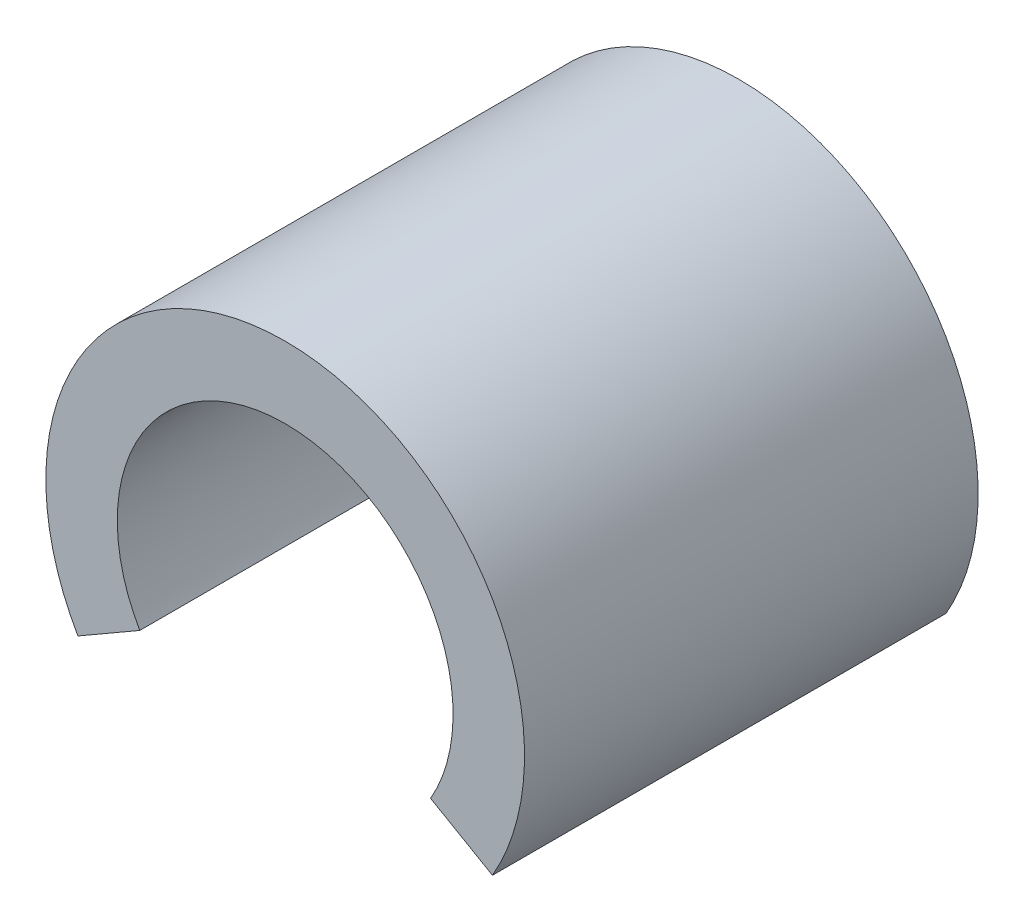
SolidWorks part; units mm, degrees
ref_plane "Front Plane" through (0, 0, 0) normal (0, 0, 1) x (1, 0, 0)
ref_plane "Top Plane" through (0, 0, 0) normal (0, 1, 0) x (1, 0, 0)
ref_plane "Right Plane" through (0, 0, 0) normal (1, 0, 0) x (0, 0, -1)
sketch "Sketch1" plane through (0, 0, 0) normal (0, 0, 1) x (1, 0, 0)
  line L0 (0, 0) -> (0, -12.4422) construction
  line L2 (-4.0703, -2.35) -> (-5.8024, -3.35)
  line L3 (4.0703, -2.35) -> (5.8024, -3.35)
  arc A0 (4.0703, -2.35) -> (-4.0703, -2.35) centre (0, 0) ccw
  arc A1 (5.8024, -3.35) -> (-5.8024, -3.35) centre (0, 0) ccw
  dimension "D1" = 9.4
  dimension "D2" = 13.4
  dimension "D3" = 60
extrude "Boss-Extrude1" add sketch "Sketch1" along normal blind 12.7
